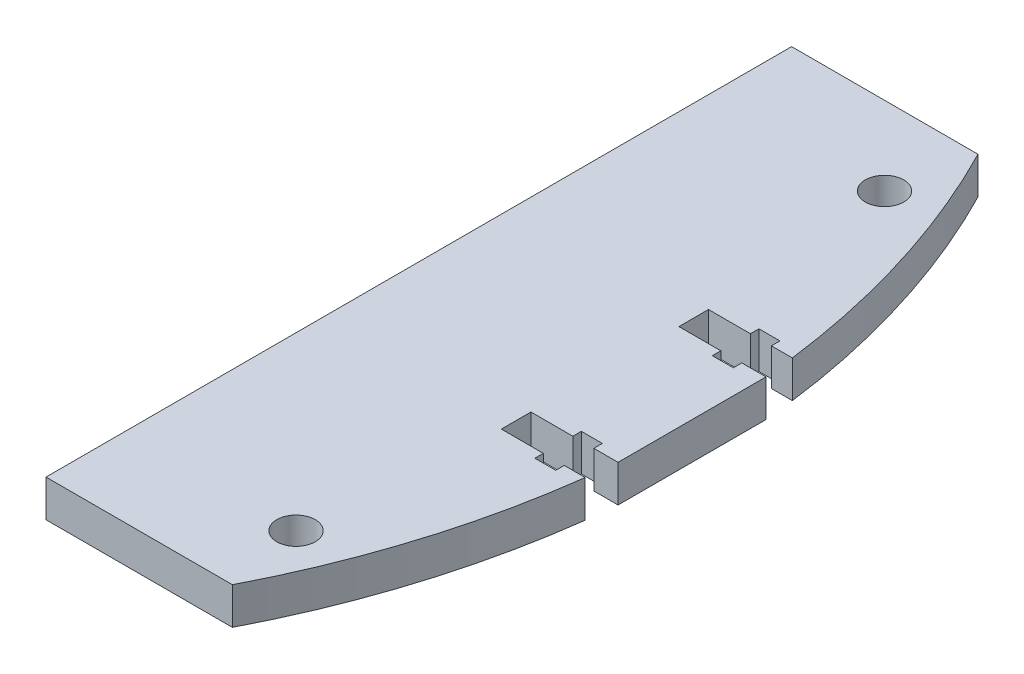
SolidWorks part; units mm, degrees
ref_plane "Front Plane" through (0, 0, 0) normal (0, 0, 1) x (1, 0, 0)
ref_plane "Top Plane" through (0, 0, 0) normal (0, 1, 0) x (1, 0, 0)
ref_plane "Right Plane" through (0, 0, 0) normal (1, 0, 0) x (0, 0, -1)
sketch "Base w/ Motor Mounts" plane through (0, 0, 0) normal (0, 1, 0) x (1, 0, 0)
  line L0 (0, 70) -> (0, -70) construction
  line L1 (0, 0) -> (70, 0) construction
  circle A0 centre (0, 0) radius 70
  dimension "D6" = 140
sketch "Standoffs (top / bottom)" plane through (0, 0, 0) normal (0, 1, 0) x (1, 0, 0)
  line L0 (0, 0) -> (64.6716, 26.7878) construction
  line L1 (0, 0) -> (49.4975, 49.4975) construction
  line L2 (0, 0) -> (26.7878, 64.6716) construction
  line L3 (0, 0) -> (70, 0) construction
  line L4 (-70, 0) -> (70, 0) construction
  line L5 (0, 0) -> (64.6716, -26.7878) construction
  line L6 (0, 0) -> (49.4975, -49.4975) construction
  line L7 (0, 0) -> (26.7878, -64.6716) construction
  line L8 (0, 70) -> (0, -70) construction
  line L9 (0, 0) -> (-26.7878, -64.6716) construction
  line L10 (0, 0) -> (-49.4975, -49.4975) construction
  line L11 (0, 0) -> (-64.6716, -26.7878) construction
  line L12 (0, 0) -> (-26.7878, 64.6716) construction
  line L13 (0, 0) -> (-49.4975, 49.4975) construction
  line L14 (0, 0) -> (-64.6716, 26.7878) construction
  circle A0 centre (0, 0) radius 70 construction
  circle A3 centre (60.976, 25.2571) radius 1.65
  circle A6 centre (60.976, -25.2571) radius 1.65
  circle A9 centre (-60.976, -25.2571) radius 1.65
  circle A12 centre (-60.976, 25.2571) radius 1.65
  circle A14 centre (0, 0) radius 70 construction
  circle A15 centre (10.5, -60.9531) radius 1.65
  circle A16 centre (-10.5, -60.9531) radius 1.65
  dimension "D4" = 3.3
  dimension "D5" = 10.5
  dimension "D6" = 21
  dimension "D1" = 22.5
  dimension "D2" = 22.5
  dimension "D3" = 22.5
sketch "Pi and Mega Standoffs" plane through (0, 0, 0) normal (0, 1, 0) x (1, 0, 0)
  line L0 (0, 70) -> (0, -70) construction
  line L1 (-19.9, 55) -> (38.1, 55) construction
  line L2 (-19.9, 55) -> (-19.9, 6) construction
  line L3 (-19.9, 6) -> (38.1, 6) construction
  line L4 (38.1, 55) -> (38.1, 6) construction
  line L5 (-19.9, 55) -> (38.1, 6) construction
  line L6 (-19.9, 6) -> (38.1, 55) construction
  line L7 (0, 0) -> (70, 0) construction
  line L8 (-38.1, -6) -> (38.1, -6) construction
  line L9 (-38.1, -6) -> (-38.1, -54.2) construction
  line L10 (-38.1, -54.2) -> (38.1, -54.2) construction
  line L11 (38.1, -6) -> (38.1, -54.2) construction
  line L12 (-38.1, -6) -> (38.1, -54.2) construction
  line L13 (-38.1, -54.2) -> (38.1, -6) construction
  circle A0 centre (-19.9, 55) radius 1.4
  circle A1 centre (38.1, 55) radius 1.4
  circle A2 centre (38.1, 6) radius 1.4
  circle A3 centre (-19.9, 6) radius 1.4
  circle A4 centre (-38.1, -54.2) radius 1.65
  circle A5 centre (-36.8, -6) radius 1.65
  circle A6 centre (38.1, -6) radius 1.65
  point P0 (-10.6204, 31.3097)
  point P11 (0, -30.1)
  dimension "D3" = 2.8
  dimension "D5" = 3.3
  dimension "D1" = 49
  dimension "D2" = 58
  dimension "D4" = 76.2
  dimension "D6" = 1.3
  dimension "D7" = 74.9
  dimension "D8" = 48.2
  dimension "D9" = 6
  dimension "D10" = 6
sketch "Sketch1" plane through (0, 0, 0) normal (0, 1, 0) x (1, 0, 0)
  line L0 (62.2575, 32) -> (46.2575, 32)
  line L1 (46.2575, 32) -> (46.2575, -32)
  line L2 (46.2575, -32) -> (62.2575, -32)
  line L3 (0, 0) -> (70, 0) construction
  line L4 (69.7114, 6.35) -> (67.6332, 6.35)
  line L9 (67.6332, 6.35) -> (67.6332, 5.62)
  line L10 (67.6332, 5.62) -> (65.8332, 5.62)
  line L11 (65.8332, 5.62) -> (65.8332, 6.35)
  line L12 (65.8332, 6.35) -> (62.2332, 6.35)
  line L13 (62.2332, 6.35) -> (62.2332, 8.89)
  line L14 (62.2332, 8.89) -> (65.8332, 8.89)
  line L15 (65.8332, 8.89) -> (65.8332, 9.62)
  line L16 (65.8332, 9.62) -> (67.6332, 9.62)
  line L17 (67.6332, 9.62) -> (67.6332, 8.89)
  line L18 (67.6332, 8.89) -> (69.4332, 8.89)
  line L19 (46.2575, 0) -> (70, 0) construction
  line L20 (67.6332, -8.89) -> (69.4332, -8.89)
  line L21 (67.6332, -9.62) -> (67.6332, -8.89)
  line L22 (65.8332, -9.62) -> (67.6332, -9.62)
  line L23 (65.8332, -8.89) -> (65.8332, -9.62)
  line L24 (62.2332, -8.89) -> (65.8332, -8.89)
  line L25 (62.2332, -6.35) -> (62.2332, -8.89)
  line L26 (65.8332, -6.35) -> (62.2332, -6.35)
  line L27 (65.8332, -5.62) -> (65.8332, -6.35)
  line L28 (67.6332, -5.62) -> (65.8332, -5.62)
  line L29 (67.6332, -6.35) -> (67.6332, -5.62)
  line L30 (69.7114, -6.35) -> (67.6332, -6.35)
  line L31 (69.7114, 6.35) -> (69.7114, -6.35)
  circle A0 centre (0, 0) radius 70 construction
  circle A2 centre (60.976, -25.2571) radius 1.65
  circle A3 centre (60.976, 25.2571) radius 1.65
  arc A5 (62.2575, 32) -> (69.4332, 8.89) centre (0, 0) cw
  arc A7 (69.4332, -8.89) -> (62.2575, -32) centre (0, 0) cw
  dimension "D9" = 3.3
  dimension "D1" = 32
  dimension "D4" = 1.8
  dimension "D6" = 4
  dimension "D7" = 2.54
  dimension "D8" = 5.62
  dimension "D10" = 16
extrude "Boss-Extrude1" add sketch "Sketch1" along normal blind 3.175
equation "\"D10@Pi and Mega Standoffs\"=\"D9@Pi and Mega Standoffs\""
